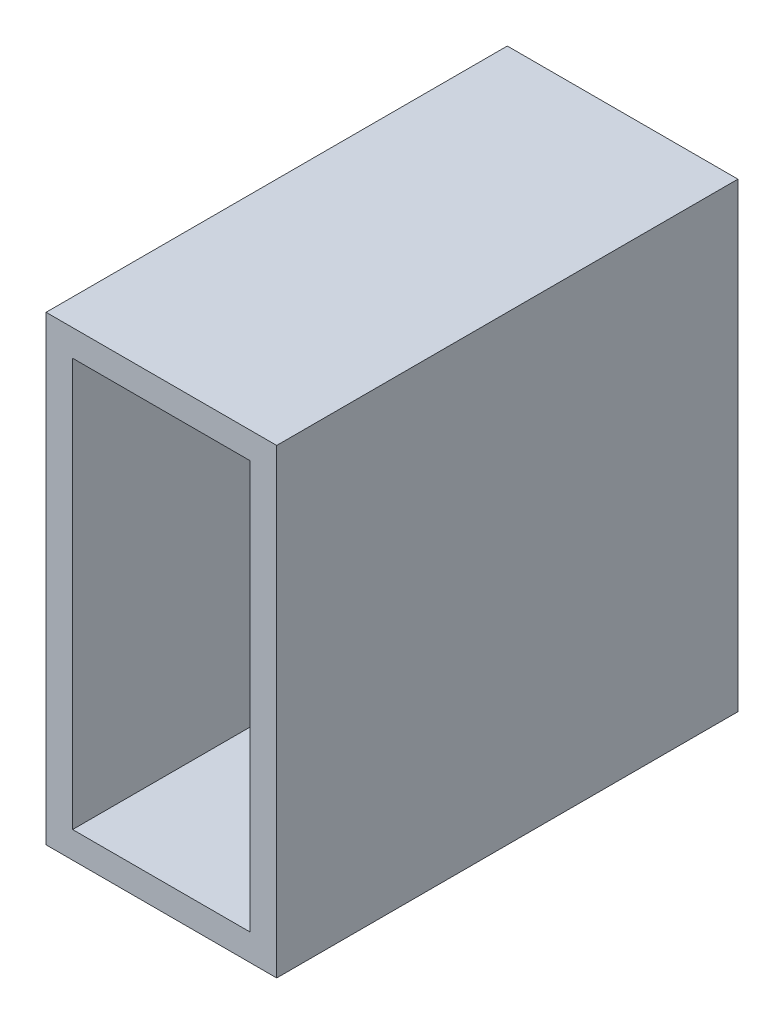
SolidWorks part; units mm, degrees
material "6061 Alloy"
ref_plane "Front Plane" through (0, 0, 0) normal (0, 0, 1) x (1, 0, 0)
ref_plane "Top Plane" through (0, 0, 0) normal (0, 1, 0) x (1, 0, 0)
ref_plane "Right Plane" through (0, 0, 0) normal (1, 0, 0) x (0, 0, -1)
sketch "Sketch1" plane through (0, 0, 0) normal (0, 0, 1) x (1, 0, 0)
  line L0 (-9.779, 22.479) -> (9.779, 22.479)
  line L1 (-12.7, -25.4) -> (12.7, -25.4)
  line L2 (-12.7, -25.4) -> (-12.7, 25.4)
  line L3 (-12.7, 25.4) -> (12.7, 25.4)
  line L4 (12.7, -25.4) -> (12.7, 25.4)
  line L5 (-12.7, -25.4) -> (12.7, 25.4) construction
  line L6 (-12.7, 25.4) -> (12.7, -25.4) construction
  line L7 (9.779, -22.479) -> (9.779, 22.479)
  line L8 (-9.779, -22.479) -> (9.779, -22.479)
  line L9 (-9.779, -22.479) -> (-9.779, 22.479)
  point P0 (0, 0)
  dimension "D1" = 25.4
  dimension "D2" = 50.8
  dimension "D3" = 2.921
extrude "Boss-Extrude1" add sketch "Sketch1" along normal blind 50.8
equation "\"length\" = 2"
equation "\"D1@Boss-Extrude1\"=\"length\""
